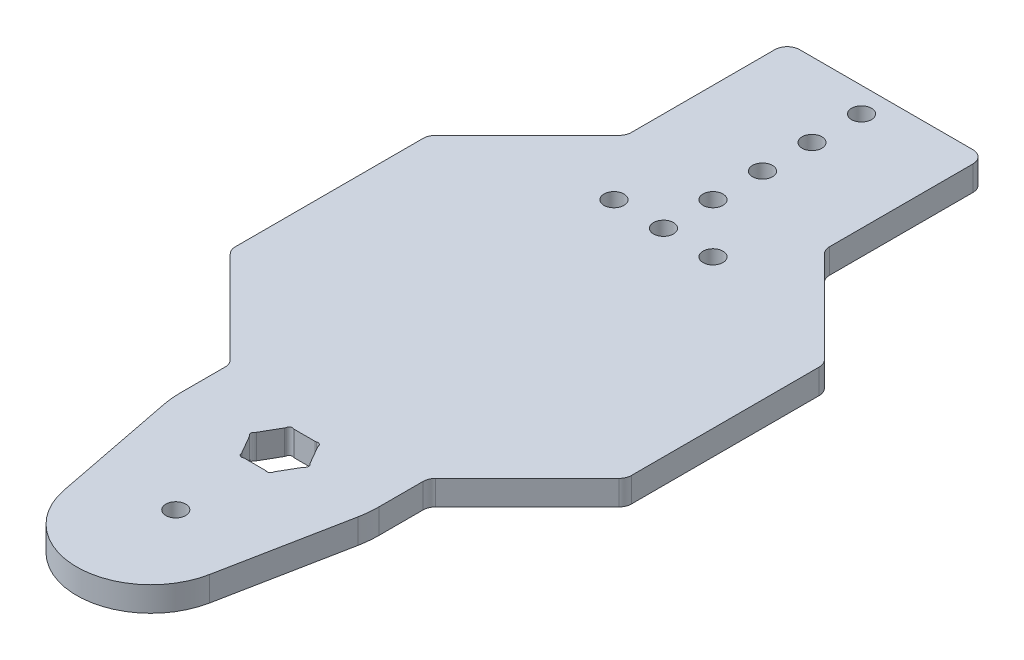
SolidWorks part; units mm, degrees
ref_plane "Front Plane" through (0, 0, 0) normal (0, 0, 1) x (1, 0, 0)
ref_plane "Top Plane" through (0, 0, 0) normal (0, 1, 0) x (1, 0, 0)
ref_plane "Right Plane" through (0, 0, 0) normal (1, 0, 0) x (0, 0, -1)
sketch "Sketch1" plane through (0, 0, 0) normal (0, 1, 0) x (1, 0, 0)
  line L0 (-26.3299, 49.8701) -> (-49.8701, 26.3299)
  line L1 (-50.8, 24.0849) -> (-50.8, -24.0849)
  line L2 (-49.8701, -26.3299) -> (-26.3299, -49.8701)
  line L3 (-25.4, -52.1151) -> (-25.4, -63.5)
  line L4 (-24.9259, -68.3846) -> (-18.6944, -100.1835)
  line L5 (18.6944, -100.1835) -> (24.9259, -68.3846)
  line L6 (25.4, -63.5) -> (25.4, -52.1151)
  line L7 (26.3299, -49.8701) -> (49.8701, -26.3299)
  line L8 (50.8, -24.0849) -> (50.8, 24.0849)
  line L9 (49.8701, 26.3299) -> (26.3299, 49.8701)
  line L10 (25.4, 52.1151) -> (25.4, 88.9)
  line L11 (22.225, 92.075) -> (-22.225, 92.075)
  line L12 (-25.4, 88.9) -> (-25.4, 52.1151)
  line L13 (-4.236, -68.99) -> (-6.8725, -64.4235)
  line L14 (-6.8725, -62.5765) -> (-4.236, -58.01)
  line L15 (-2.6365, -57.0865) -> (2.6365, -57.0865)
  line L16 (4.236, -58.01) -> (6.8725, -62.5765)
  line L17 (6.8725, -64.4235) -> (4.236, -68.99)
  line L18 (2.6365, -69.9135) -> (-2.6365, -69.9135)
  arc A0 (-49.8701, 26.3299) -> (-50.8, 24.0849) centre (-47.625, 24.0849) ccw
  arc A1 (-50.8, -24.0849) -> (-49.8701, -26.3299) centre (-47.625, -24.0849) ccw
  arc A2 (-26.3299, -49.8701) -> (-25.4, -52.1151) centre (-28.575, -52.1151) cw
  arc A3 (-25.4, -63.5) -> (-24.9259, -68.3846) centre (0, -63.5) ccw
  arc A4 (-18.6944, -100.1835) -> (18.6944, -100.1835) centre (0, -96.52) ccw
  arc A5 (24.9259, -68.3846) -> (25.4, -63.5) centre (0, -63.5) ccw
  arc A6 (25.4, -52.1151) -> (26.3299, -49.8701) centre (28.575, -52.1151) cw
  arc A7 (49.8701, -26.3299) -> (50.8, -24.0849) centre (47.625, -24.0849) ccw
  arc A8 (50.8, 24.0849) -> (49.8701, 26.3299) centre (47.625, 24.0849) ccw
  arc A9 (26.3299, 49.8701) -> (25.4, 52.1151) centre (28.575, 52.1151) cw
  arc A10 (25.4, 88.9) -> (22.225, 92.075) centre (22.225, 88.9) ccw
  arc A11 (-22.225, 92.075) -> (-25.4, 88.9) centre (-22.225, 88.9) ccw
  arc A12 (-25.4, 52.1151) -> (-26.3299, 49.8701) centre (-28.575, 52.1151) cw
  circle A13 centre (0, -90.17) radius 2.5527
  circle A14 centre (0, 85.725) radius 2.5527
  circle A15 centre (0, 73.025) radius 2.5527
  circle A16 centre (0, 60.325) radius 2.5527
  circle A17 centre (0, 47.625) radius 2.5527
  circle A18 centre (0, 34.925) radius 2.5527
  circle A19 centre (-12.7, 34.925) radius 2.5527
  circle A20 centre (12.7, 34.925) radius 2.5527
  arc A21 (-6.8725, -64.4235) -> (-7.0678, -64.1975) centre (-7.5599, -64.8203) ccw
  arc A22 (-7.0678, -64.1975) -> (-7.0678, -62.8025) centre (-6.5167, -63.5) cw
  arc A23 (-7.0678, -62.8025) -> (-6.8725, -62.5765) centre (-7.5599, -62.1797) ccw
  arc A24 (-4.236, -58.01) -> (-4.138, -57.7279) centre (-4.9234, -57.6131) ccw
  arc A25 (-4.138, -57.7279) -> (-2.9298, -57.0303) centre (-3.2583, -57.8564) cw
  arc A26 (-2.9298, -57.0303) -> (-2.6365, -57.0865) centre (-2.6365, -56.2928) ccw
  arc A27 (2.6365, -57.0865) -> (2.9298, -57.0303) centre (2.6365, -56.2928) ccw
  arc A28 (2.9298, -57.0303) -> (4.138, -57.7279) centre (3.2583, -57.8564) cw
  arc A29 (4.138, -57.7279) -> (4.236, -58.01) centre (4.9234, -57.6131) ccw
  arc A30 (6.8725, -62.5765) -> (7.0678, -62.8025) centre (7.5599, -62.1797) ccw
  arc A31 (7.0678, -62.8025) -> (7.0678, -64.1975) centre (6.5167, -63.5) cw
  arc A32 (7.0678, -64.1975) -> (6.8725, -64.4235) centre (7.5599, -64.8203) ccw
  arc A33 (4.236, -68.99) -> (4.138, -69.2721) centre (4.9234, -69.3869) ccw
  arc A34 (4.138, -69.2721) -> (2.9298, -69.9697) centre (3.2583, -69.1436) cw
  arc A35 (2.9298, -69.9697) -> (2.6365, -69.9135) centre (2.6365, -70.7073) ccw
  arc A36 (-2.6365, -69.9135) -> (-2.9298, -69.9697) centre (-2.6365, -70.7073) ccw
  arc A37 (-2.9298, -69.9697) -> (-4.138, -69.2721) centre (-3.2583, -69.1436) cw
  arc A38 (-4.138, -69.2721) -> (-4.236, -68.99) centre (-4.9234, -69.3869) ccw
  dimension "D1" = 5.1054
  dimension "D2" = 5.1054
  dimension "D3" = 5.1054
  dimension "D4" = 5.1054
  dimension "D5" = 5.1054
  dimension "D6" = 5.1054
  dimension "D7" = 5.1054
  dimension "D8" = 5.1054
  dimension "D9" = 3.175
  dimension "D10" = 3.175
  dimension "D11" = 38.1
  dimension "D12" = 43.2401
  dimension "D13" = 6.35
  dimension "D14" = 19.05
  dimension "D15" = 31.75
  dimension "D16" = 44.45
  dimension "D17" = 57.15
  dimension "D18" = 182.245
  dimension "D32" = 63.5
extrude "Boss-Extrude1" add sketch "Sketch1" against normal blind 6.35
